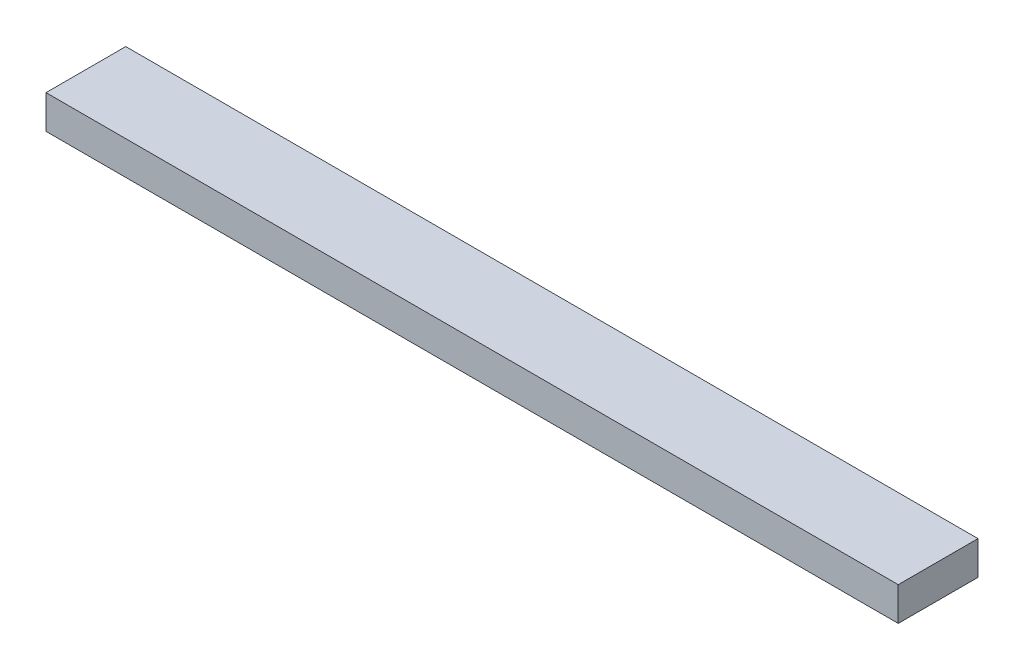
SolidWorks part; units mm, degrees
ref_plane "Front Plane" through (0, 0, 0) normal (0, 0, 1) x (1, 0, 0)
ref_plane "Top Plane" through (0, 0, 0) normal (0, 1, 0) x (1, 0, 0)
ref_plane "Right Plane" through (0, 0, 0) normal (1, 0, 0) x (0, 0, -1)
sketch "Sketch1" plane through (0, 0, 0) normal (0, 1, 0) x (1, 0, 0)
  line L1 (-50.75, 4.75) -> (50.75, 4.75)
  line L2 (-50.75, 4.75) -> (-50.75, -4.75)
  line L3 (-50.75, -4.75) -> (50.75, -4.75)
  line L4 (50.75, 4.75) -> (50.75, -4.75)
  line L5 (-50.75, 4.75) -> (50.75, -4.75) construction
  line L6 (-50.75, -4.75) -> (50.75, 4.75) construction
  point P0 (0, 0)
  dimension "D1" = 101.5
  dimension "D2" = 9.5
extrude "Boss-Extrude1" add sketch "Sketch1" along normal blind 4
